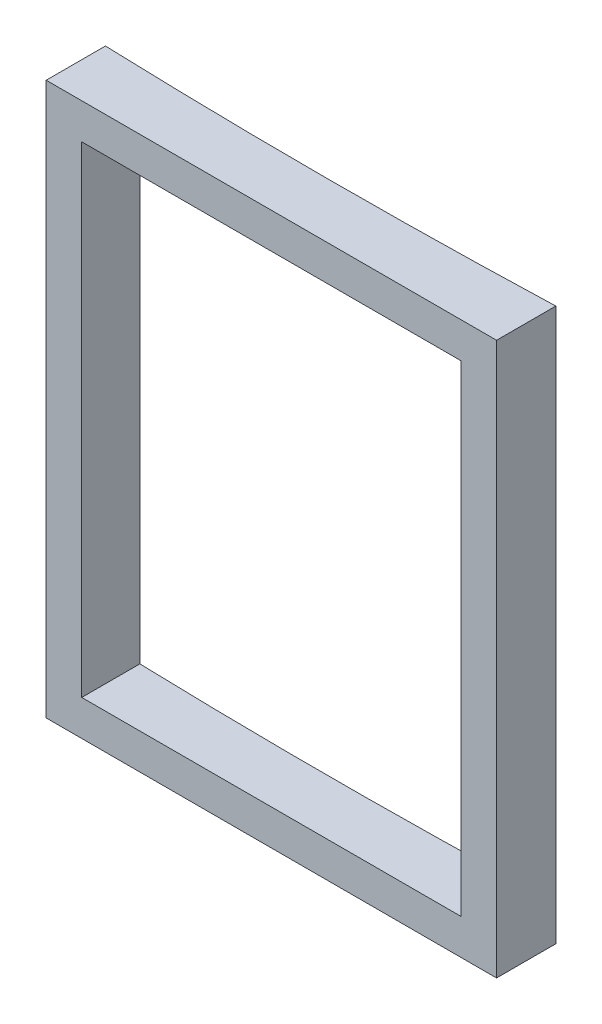
SolidWorks part; units mm, degrees
ref_plane "Front Plane" through (0, 0, 0) normal (0, 0, 1) x (1, 0, 0)
ref_plane "Top Plane" through (0, 0, 0) normal (0, 1, 0) x (1, 0, 0)
ref_plane "Right Plane" through (0, 0, 0) normal (1, 0, 0) x (0, 0, -1)
sketch "Sketch2" plane through (0, 0, 0) normal (0, 1, 0) x (1, 0, 0)
  line L0 (-6692.1861, -5017.368) -> (-6692.1861, -5267.368)
  line L1 (-8592.1861, -5017.368) -> (-8592.1861, -5267.368)
  line L2 (-8592.1861, -5267.368) -> (-6692.1861, -5267.368)
  arc A0 (-6692.1861, -5017.368) -> (-8592.1861, -5017.368) centre (-7642.1861, 22466.218) cw
  point P4 (4390.1059, 1014.4814)
  point P5 (-6692.1861, 1014.4814)
  dimension "D1" = 27500
  dimension "D2" = 1900
  dimension "D3" = 250
extrude "Boss-Extrude1" add sketch "Sketch2" along normal blind 2330
sketch "Sketch3" plane through (0, 0, 5267.368) normal (0, 0, 1) x (1, 0, 0)
  line L0 (-8442.1861, 2180) -> (-6842.1861, 2180)
  line L1 (-6842.1861, 2180) -> (-6842.1861, 150)
  line L2 (-6842.1861, 150) -> (-8442.1861, 150)
  line L3 (-8442.1861, 150) -> (-8442.1861, 2180)
  line L4 (-6692.1861, 2330) -> (-6692.1861, 0) construction
  line L5 (-8592.1861, 0) -> (-6692.1861, 0) construction
  line L6 (-8592.1861, 2330) -> (-6692.1861, 2330) construction
  point P3 (-7642.1861, 2180)
  dimension "D1" = 1600
  dimension "D2" = 150
  dimension "D3" = 150
  dimension "D4" = 150
  dimension "D5" = 2030
extrude "Cut-Extrude1" cut sketch "Sketch3" against normal blind 3000
